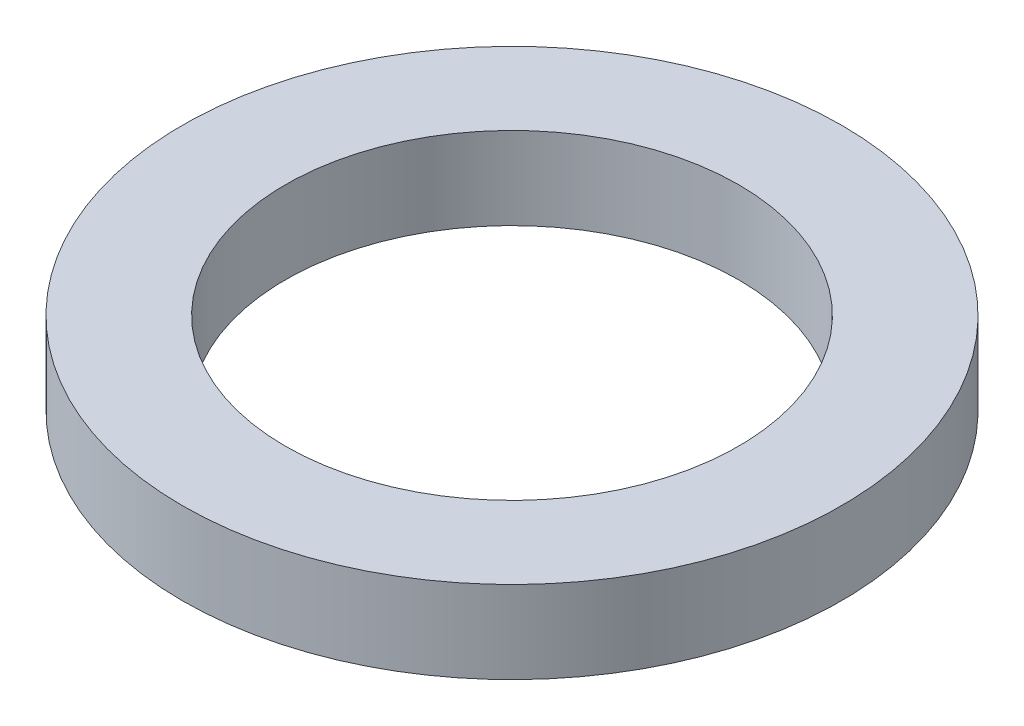
SolidWorks part; units mm, degrees
ref_plane "Front Plane" through (0, 0, 0) normal (0, 0, 1) x (1, 0, 0)
ref_plane "Top Plane" through (0, 0, 0) normal (0, 1, 0) x (1, 0, 0)
ref_plane "Right Plane" through (0, 0, 0) normal (1, 0, 0) x (0, 0, -1)
sketch "Sketch1" plane through (0, 0, 0) normal (0, 1, 0) x (1, 0, 0)
  circle A0 centre (0, 0) radius 4
  circle A1 centre (0, 0) radius 2.75
  dimension "D1" = 8
extrude "Boss-Extrude1" add sketch "Sketch1" along normal blind 1
